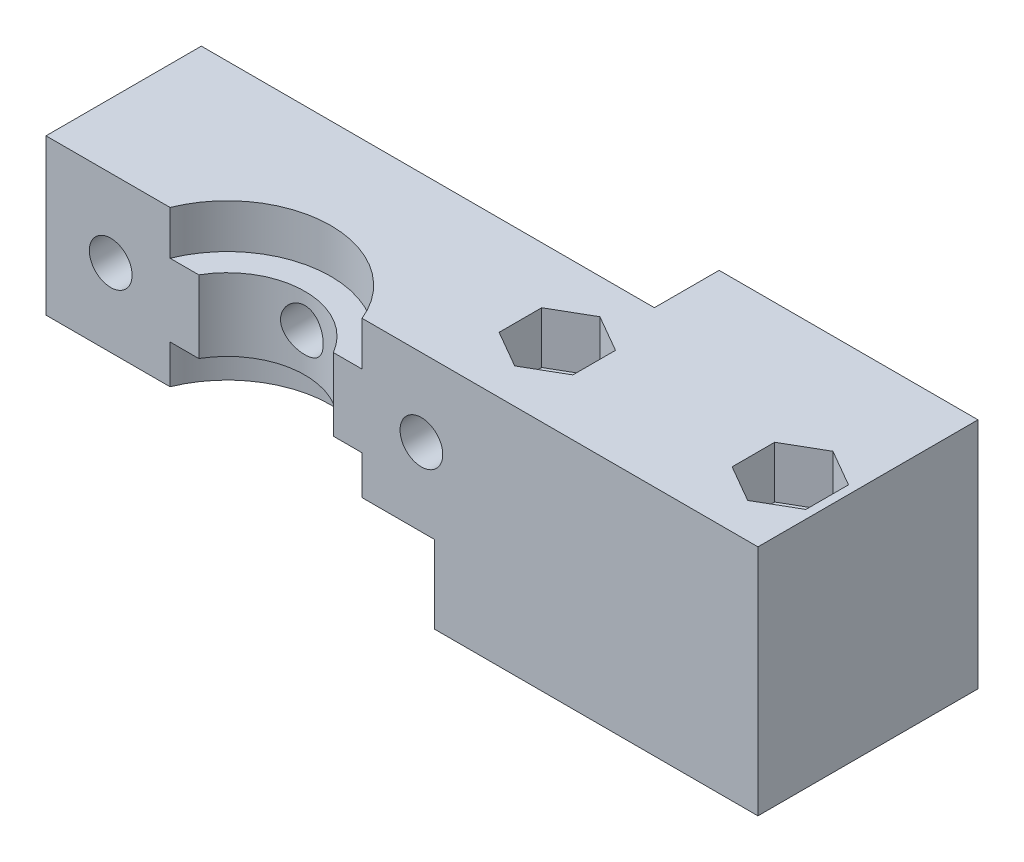
SolidWorks part; units mm, degrees
ref_plane "前视基准面" through (0, 0, 0) normal (0, 0, 1) x (1, 0, 0)
ref_plane "上视基准面" through (0, 0, 0) normal (0, 1, 0) x (1, 0, 0)
ref_plane "右视基准面" through (0, 0, 0) normal (1, 0, 0) x (0, 0, -1)
sketch "草图1" plane through (0, 0, 0) normal (0, 1, 0) x (1, 0, 0)
  line L1 (17, 3) -> (17, 15)
  line L2 (17, 15) -> (-17, 15)
  line L3 (-17, 15) -> (-17, 3)
  line L4 (0, 0) -> (0, 17.0207) construction
  line L6 (-1024.4317, 0) -> (-17, 0) construction
  line L10 (-7.4162, 3) -> (-17, 3)
  line L12 (17, 3) -> (7.4162, 3)
  arc A0 (7.4162, 3) -> (-7.4162, 3) centre (0, 0) ccw
  dimension "D4" = 16
  dimension "D1" = 12
  dimension "D2" = 15
  dimension "D3" = 17
extrude "凸台-拉伸1" add sketch "草图1" along normal blind 3
sketch "草图2" plane through (0, 3, 0) normal (0, 1, 0) x (1, 0, 0)
  line L5 (-17, 15) -> (-17, 3)
  line L6 (7.4162, 3) -> (17, 3)
  line L7 (5.1962, 3) -> (17, 3)
  line L8 (17, 3) -> (17, 15)
  line L9 (17, 15) -> (-17, 15)
  line L10 (-17, 15) -> (-17, 3)
  line L13 (17, 3) -> (17, 15)
  line L14 (17, 15) -> (-17, 15)
  line L15 (-17, 3) -> (-7.4162, 3)
  line L16 (-17, 3) -> (-5.1962, 3)
  arc A0 (5.1962, 3) -> (-5.1962, 3) centre (0, 0) ccw
  arc A1 (7.4162, 3) -> (-7.4162, 3) centre (0, 0) ccw
  dimension "D2" = 12
  dimension "D1" = 0
extrude "凸台-拉伸2" add sketch "草图2" along normal blind 5.6
sketch "草图3" plane through (0, 8.6, 0) normal (0, 1, 0) x (1, 0, 0)
  line L5 (17, 15) -> (-17, 15)
  line L6 (-17, 15) -> (-17, 3)
  line L7 (-17, 3) -> (-5.1962, 3)
  line L8 (-17, 3) -> (-7.4162, 3)
  line L9 (17, 3) -> (17, 15)
  line L10 (17, 15) -> (-17, 15)
  line L11 (-17, 15) -> (-17, 3)
  line L14 (17, 3) -> (17, 15)
  line L15 (5.1962, 3) -> (17, 3)
  line L16 (7.4162, 3) -> (17, 3)
  arc A0 (7.4162, 3) -> (-7.4162, 3) centre (0, 0) ccw
  arc A1 (5.1962, 3) -> (-5.1962, 3) centre (0, 0) ccw
  dimension "D2" = 16
  dimension "D1" = 0
extrude "凸台-拉伸3" add sketch "草图3" along normal blind 3.4
sketch "草图5" plane through (0, 12, 0) normal (0, -1, 0) x (1, 0, 0)
  line L0 (13, -3) -> (13, -15)
  line L1 (17, -3) -> (17, -15) construction
  line L2 (13, -15) -> (38, -15)
  line L3 (13, -3) -> (38, -3)
  line L4 (38, -3) -> (38, -15)
  line L5 (17, -15) -> (-17, -15) construction
  dimension "D1" = 4
  dimension "D2" = 25
  dimension "D3" = 12
extrude "凸台-拉伸4" add sketch "草图5" along normal blind 18
sketch "草图8" plane through (0, 0, -15) normal (0, 0, -1) x (-1, 0, 0)
  line L0 (-18, 12) -> (-18, -6)
  line L6 (17, 12) -> (-38, 12)
  line L7 (-38, 12) -> (-38, -6)
  line L8 (-38, -6) -> (-13, -6)
  line L9 (-13, -6) -> (-13, 0)
  line L10 (-13, 0) -> (17, 0)
  line L11 (17, 0) -> (17, 12)
  line L12 (-18, 12) -> (-38, 12)
  line L13 (-38, 12) -> (-38, -6)
  line L14 (-38, -6) -> (-18, -6)
  dimension "D2" = 20
  dimension "D1" = 0
extrude "凸台-拉伸5" add sketch "草图8" along normal blind 5
sketch "草图4" plane through (0, 0, -15) normal (0, 0, 1) x (1, 0, 0)
  line L1 (-7.4162, 0) -> (7.4162, 0) construction
  circle A0 centre (-12, 6) radius 1.65
  circle A1 centre (12, 6) radius 1.65
  circle A2 centre (0, 6) radius 1.65
  dimension "D1" = 3.3
  dimension "D2" = 3.3
  dimension "D7" = 3.3
  dimension "D6" = 12
  dimension "D8" = 6
  dimension "D9" = 12
extrude "切除-拉伸1" cut sketch "草图4" along normal through all
sketch "草图6" plane through (0, -6, 0) normal (0, -1, 0) x (1, 0, 0)
  line L0 (13, -15) -> (18, -15) construction
  line L1 (13, -3) -> (13, -15) construction
  circle A0 centre (16.5, -9) radius 1.75
  circle A1 centre (34.5, -9) radius 1.75
  dimension "D1" = 3.5
  dimension "D2" = 3.5
  dimension "D3" = 6
  dimension "D4" = 6
  dimension "D5" = 3.5
  dimension "D6" = 18
extrude "切除-拉伸2" cut sketch "草图6" against normal through all
sketch "草图7" plane through (0, 12, 0) normal (0, 1, 0) x (1, 0, 0)
  line L0 (38, 20) -> (38, 3) construction
  line L1 (16.5, 5.7091) -> (19.35, 7.3546)
  line L2 (19.35, 7.3546) -> (19.35, 10.6454)
  line L3 (19.35, 10.6454) -> (16.5, 12.2909)
  line L4 (16.5, 12.2909) -> (13.65, 10.6454)
  line L5 (13.65, 10.6454) -> (13.65, 7.3546)
  line L6 (13.65, 7.3546) -> (16.5, 5.7091)
  line L7 (34.5, 5.7091) -> (37.35, 7.3546)
  line L8 (37.35, 7.3546) -> (37.35, 10.6454)
  line L9 (37.35, 10.6454) -> (34.5, 12.2909)
  line L10 (34.5, 12.2909) -> (31.65, 10.6454)
  line L11 (31.65, 10.6454) -> (31.65, 7.3546)
  line L12 (31.65, 7.3546) -> (34.5, 5.7091)
  circle A0 centre (16.5, 9) radius 2.85 construction
  circle A1 centre (34.5, 9) radius 2.85 construction
  dimension "D1" = 5.7
  dimension "D2" = 5.7
extrude "切除-拉伸3" cut sketch "草图7" against normal blind 4
